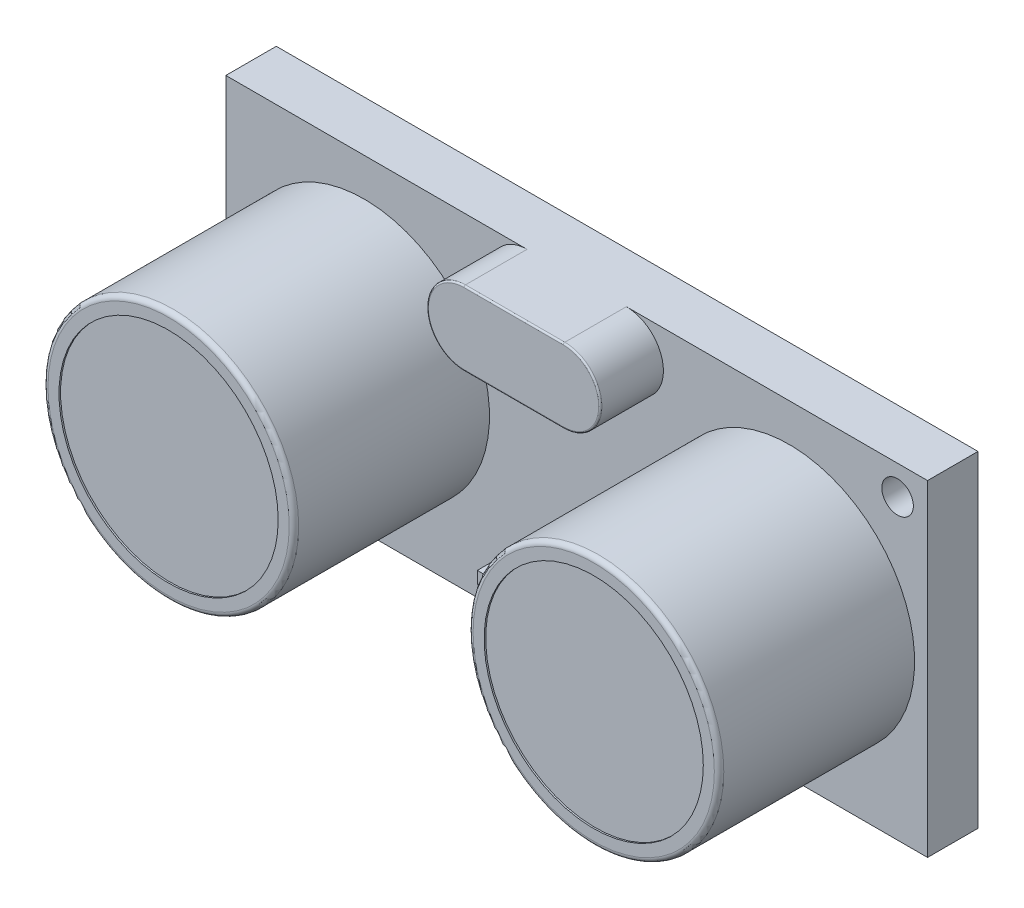
SolidWorks part; units mm, degrees
ref_plane "Front" through (0, 0, 0) normal (0, 0, 1) x (1, 0, 0)
ref_plane "Top" through (0, 0, 0) normal (0, 1, 0) x (1, 0, 0)
ref_plane "Right" through (0, 0, 0) normal (1, 0, 0) x (0, 0, -1)
sketch "Эскиз1" plane through (0, 0, 0) normal (0, 0, 1) x (1, 0, 0)
  line L1 (-22.25, -10.35) -> (22.25, -10.35)
  line L2 (-22.25, -10.35) -> (-22.25, 10.35)
  line L3 (-22.25, 10.35) -> (22.25, 10.35)
  line L4 (22.25, -10.35) -> (22.25, 10.35)
  line L5 (-22.25, -10.35) -> (22.25, 10.35) construction
  line L6 (-22.25, 10.35) -> (22.25, -10.35) construction
  point P0 (0, 0)
  dimension "D1" = 44.5
  dimension "D2" = 20.7
extrude "Бобышка-Вытянуть1" add sketch "Эскиз1" along normal blind 3.2
sketch "Эскиз2" plane through (0, 0, 3.2) normal (0, 0, 1) x (1, 0, 0)
  line L0 (-3.15, 8) -> (3.15, 8) construction
  line L1 (-3.15, 10.35) -> (3.15, 10.35)
  line L2 (-3.15, 5.65) -> (3.15, 5.65)
  line L3 (22.25, 10.35) -> (-22.25, 10.35) construction
  line L4 (0, 8) -> (0, 10.35) construction
  arc A0 (-3.15, 10.35) -> (-3.15, 5.65) centre (-3.15, 8) ccw
  arc A1 (3.15, 5.65) -> (3.15, 10.35) centre (3.15, 8) ccw
  point P2 (0, 8)
  dimension "D1" = 2.35
  dimension "D2" = 6.3
extrude "Бобышка-Вытянуть2" add sketch "Эскиз2" along normal blind 4
fillet "Скругление1" radius 0.1 4 edges at (0, 10.35, 7.2) (5.5, 8, 7.2) (0, 5.65, 7.2) (-5.5, 8, 7.2)
sketch "Эскиз3" plane through (0, 0, 3.2) normal (0, 0, 1) x (1, 0, 0)
  line L0 (-13.48, 0) -> (13.48, 0) construction
  circle A0 centre (-13.48, 0) radius 7.95
  circle A1 centre (13.48, 0) radius 7.95
  dimension "D2" = 15.9
  dimension "D3" = 26.96
extrude "Бобышка-Вытянуть3" add sketch "Эскиз3" along normal blind 12.4
sketch "Эскиз4" plane through (0, 0, 15.6) normal (0, 0, 1) x (1, 0, 0)
  circle A0 centre (-13.48, 0) radius 6.95
  circle A1 centre (13.48, 0) radius 6.95
  circle A2 centre (-13.48, 0) radius 7.95 construction
  circle A3 centre (13.48, 0) radius 7.95 construction
  dimension "D1" = 1
  dimension "D2" = 1
extrude "Вырез-Вытянуть1" cut sketch "Эскиз4" against normal blind 0.1
fillet "Скругление2" radius 0.3 2 edges at (21.43, 0, 15.6) (-5.53, 0, 15.6)
sketch "Эскиз5" plane through (0, 0, 3.2) normal (0, 0, 1) x (1, 0, 0)
  line L1 (-5.3025, -7.8599) -> (5.3025, -7.8599)
  line L2 (-5.3025, -7.8599) -> (-5.3025, -8.6107)
  line L3 (-5.3025, -8.6107) -> (5.3025, -8.6107)
  line L4 (5.3025, -7.8599) -> (5.3025, -8.6107)
  line L5 (-5.3025, -7.8599) -> (5.3025, -8.6107) construction
  line L6 (-5.3025, -8.6107) -> (5.3025, -7.8599) construction
  point P0 (0, -8.2353)
extrude "Бобышка-Вытянуть4" add sketch "Эскиз5" along normal blind 1
sketch "Эскиз6" plane through (0, 0, 0) normal (0, 0, -1) x (-1, 0, 0)
  line L1 (-5.15, -7.85) -> (5.15, -7.85)
  line L2 (-5.15, -7.85) -> (-5.15, -10.35)
  line L3 (-5.15, -10.35) -> (5.15, -10.35)
  line L4 (5.15, -7.85) -> (5.15, -10.35)
  line L5 (-5.15, -7.85) -> (5.15, -10.35) construction
  line L6 (-5.15, -10.35) -> (5.15, -7.85) construction
  line L7 (22.25, -10.35) -> (-22.25, -10.35) construction
  point P0 (0, -9.1)
  dimension "D1" = 2.5
  dimension "D2" = 10.3
extrude "Бобышка-Вытянуть5" add sketch "Эскиз6" along normal blind 4.5 separate body
sketch "Эскиз7" plane through (0, -10.35, 0) normal (0, -1, 0) x (1, 0, 0)
  circle A0 centre (-3.8948, -3.5331) radius 0.6009
  circle A1 centre (-1.3948, -3.5331) radius 0.6009
  circle A2 centre (1.1052, -3.5331) radius 0.6009
  circle A3 centre (3.6052, -3.5331) radius 0.6009
  dimension "D1" = 4
extrude "Бобышка-Вытянуть6" add sketch "Эскиз7" along normal blind 8
sketch "Эскиз8" plane through (0, 0, 0) normal (0, 0, -1) x (-1, 0, 0)
  line L0 (-21.35, 8.5) -> (-21.35, 9.5) construction
  line L1 (-22.25, -10.35) -> (-22.25, 10.35) construction
  line L2 (-20.35, 9.5) -> (-17.149, 9.5) construction
  line L4 (0, 0) -> (0, 3.2463) construction
  line L5 (20.35, 9.5) -> (17.149, 9.5) construction
  line L7 (-22.25, 0) -> (-14.0289, 0) construction
  line L8 (22.075, -8.75) -> (22.075, -9.575) construction
  line L9 (20.35, -9.5) -> (17.149, -9.5) construction
  line L10 (-20.35, -9.5) -> (-17.149, -9.5) construction
  line L11 (-21.35, -8.5) -> (-21.35, -9.5) construction
  line L12 (20.35, 8.5) -> (-20.35, 8.5) construction
  line L13 (0, 0) -> (0, 8.5) construction
  circle A0 centre (-20.35, 8.5) radius 1
  circle A2 centre (20.35, -8.5) radius 1
  dimension "D1" = 2
  dimension "D3" = 17
  dimension "D2" = 40.7
extrude "Вырез-Вытянуть2" cut sketch "Эскиз8" against normal blind 10
